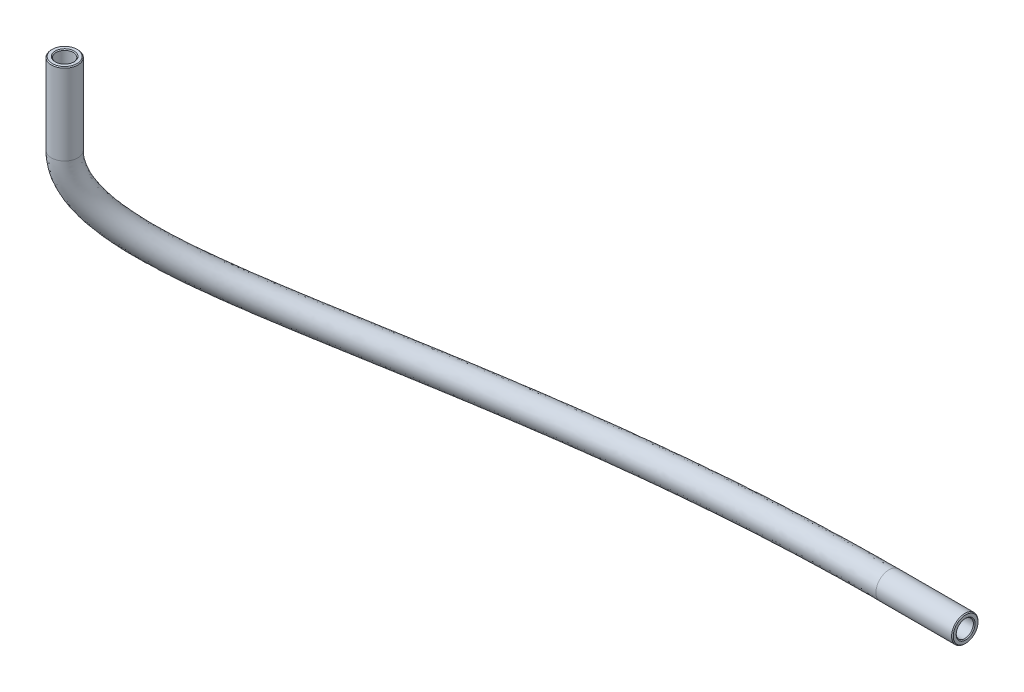
SolidWorks part; units mm, degrees
ref_plane "Front Plane" through (0, 0, 0) normal (0, 0, 1) x (1, 0, 0)
ref_plane "Top Plane" through (0, 0, 0) normal (0, 1, 0) x (1, 0, 0)
ref_plane "Right Plane" through (0, 0, 0) normal (1, 0, 0) x (0, 0, -1)
sketch3d "3DSketch2"
  line L0 (146.325, -62.025, 13.85) -> (146.325, -74.325, 13.85)
  line L1 (249.105, -102.4823, -19.725) -> (237.525, -102.4823, -19.725)
  spline S0 degree 3 poles (237.525, -102.4823, -19.725) (204.493, -102.4823, -19.725) (160.9079, -96.1897, -2.9375) (146.325, -82.0158, 13.85) (146.325, -74.325, 13.85) knots 0 0 0 0 0.535744 1 1 1 1
sketch "Sketch1" plane through (239.725, 0, 0) normal (-1, 0, 0) x (0, 0, 1)
  circle A0 centre (-19.725, -102.4823) radius 2
  circle A1 centre (-19.725, -102.4823) radius 1.3
  circle A2 centre (-19.725, -102.4823) radius 3.5386 construction
  dimension "D1" = 2.6
  dimension "D2" = 4
sweep "Sweep1" add profiles "Sketch1" path "3DSketch2"
chamfer "Chamfer1" distance 0.127 angle 45 4 edges at (145.8677, -62.025, 15.797) (146.0278, -62.025, 15.1156) (249.105, -104.4823, -19.725) (249.105, -103.7823, -19.725)
